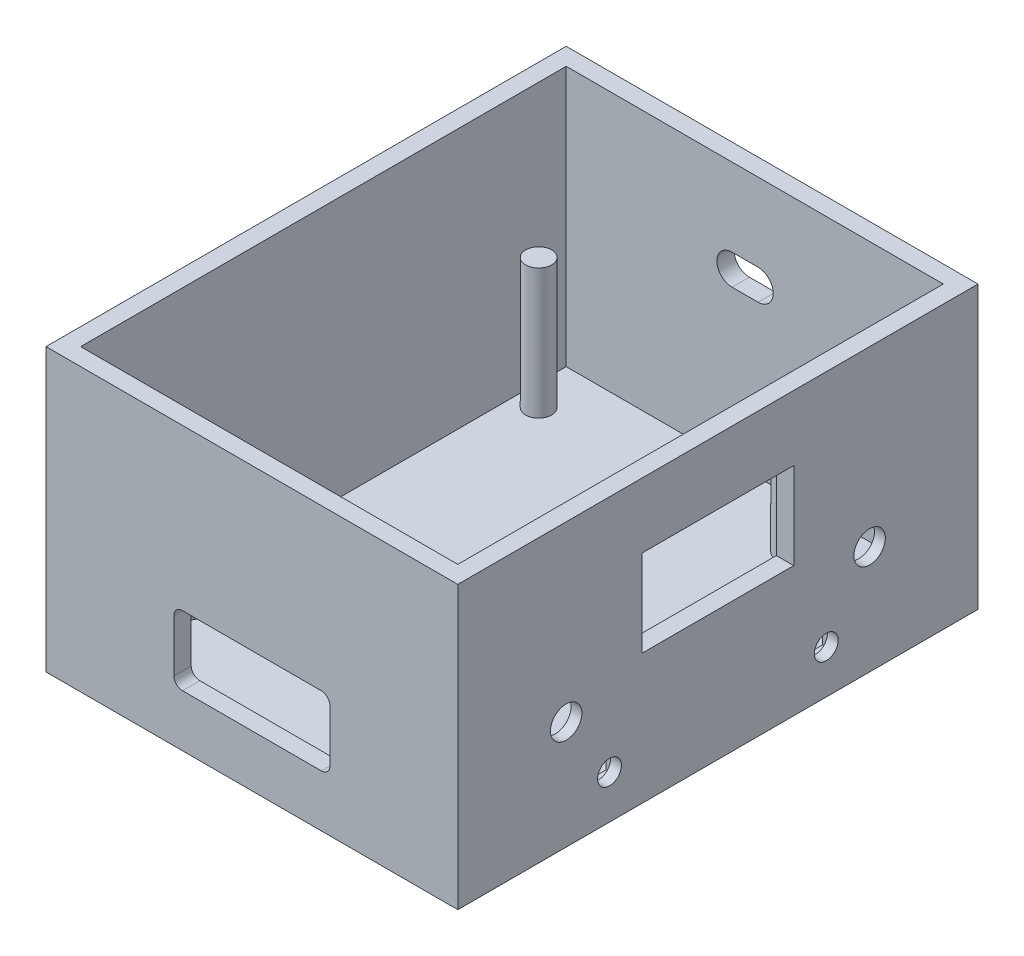
SolidWorks part; units mm, degrees
ref_plane "Front Plane" through (0, 0, 0) normal (0, 0, 1) x (1, 0, 0)
ref_plane "Top Plane" through (0, 0, 0) normal (0, 1, 0) x (1, 0, 0)
ref_plane "Right Plane" through (0, 0, 0) normal (1, 0, 0) x (0, 0, -1)
sketch "Sketch1" plane through (0, 0, 0) normal (0, 1, 0) x (1, 0, 0)
  line L1 (-47.5, -60) -> (47.5, -60)
  line L2 (-47.5, -60) -> (-47.5, 60)
  line L3 (-47.5, 60) -> (47.5, 60)
  line L4 (47.5, -60) -> (47.5, 60)
  line L5 (-47.5, -60) -> (47.5, 60) construction
  line L6 (-47.5, 60) -> (47.5, -60) construction
  point P0 (0, 0)
  dimension "D1" = 120
  dimension "D2" = 95
extrude "base dimensions" add sketch "Sketch1" along normal blind 5
sketch "Sketch2" plane through (0, 5, 0) normal (0, 1, 0) x (1, 0, 0)
  line L0 (47.5, -60) -> (47.5, 60) construction
  line L1 (-47.5, -60) -> (47.5, -60) construction
  line L2 (-47.5, 60) -> (-47.5, -60) construction
  line L3 (47.5, 60) -> (-47.5, 60) construction
  line L4 (47.5, -60) -> (47.5, 60)
  line L5 (-47.5, -60) -> (47.5, -60)
  line L6 (-47.5, 60) -> (-47.5, -60)
  line L7 (47.5, 60) -> (-47.5, 60)
  line L9 (-43.5, -56) -> (43.5, -56)
  line L10 (-43.5, -56) -> (-43.5, 56)
  line L11 (-43.5, 56) -> (43.5, 56)
  line L12 (43.5, -56) -> (43.5, 56)
  line L13 (-43.5, -56) -> (43.5, 56) construction
  line L14 (-43.5, 56) -> (43.5, -56) construction
  point P4 (0, 0)
  dimension "D1" = 4
  dimension "D2" = 4
extrude "wall height and depth" add sketch "Sketch2" along normal blind 60
sketch "Sketch3" plane through (0, 5, 0) normal (0, 1, 0) x (1, 0, 0)
  line L0 (-43.5, 56) -> (-43.5, -56) construction
  line L1 (-43.5, -56) -> (43.5, -56) construction
  circle A0 centre (-38.5, 44.645) radius 3
  circle A1 centre (-38.5, -36) radius 3
  circle A2 centre (32.62, -36) radius 3
  circle A3 centre (19.285, 44.645) radius 3
  dimension "D4" = 6
  dimension "D1" = 57.785
  dimension "D2" = 71.12
  dimension "D3" = 80.645
  dimension "D5" = 5
  dimension "D6" = 20
extrude "support pegs" add sketch "Sketch3" along normal blind 30
sketch "Sketch4" plane through (47.5, 0, 0) normal (1, 0, 0) x (0, 0, -1)
  line L0 (0, 71.0913) -> (0, -6.0913) construction
  line L1 (-17.5, 50) -> (17.5, 50)
  line L2 (-17.5, 50) -> (-17.5, 30)
  line L3 (-17.5, 30) -> (17.5, 30)
  line L4 (17.5, 50) -> (17.5, 30)
  line L5 (-17.5, 50) -> (17.5, 30) construction
  line L6 (-17.5, 30) -> (17.5, 50) construction
  line L7 (52.25, 0) -> (-52.25, 0) construction
  line L8 (-60, 65) -> (60, 65) construction
  circle A0 centre (-35, 25) radius 3.625
  circle A1 centre (-25, 10) radius 2.75
  circle A2 centre (25, 10) radius 2.75
  circle A3 centre (35, 25) radius 3.625
  point P0 (0, 40)
  point P12 (25, 10)
  dimension "D3" = 7.25
  dimension "D4" = 5.5
  dimension "D1" = 25
  dimension "D2" = 35
  dimension "D5" = 10
  dimension "D6" = 25
  dimension "D7" = 20
  dimension "D8" = 35
  dimension "D9" = 25
extrude "front holes" cut sketch "Sketch4" against normal up to surface (4 mm away) up to face at (43.5, 35, 0)
sketch "Sketch6" plane through (43.5, 0, 0) normal (-1, 0, 0) x (0, 0, 1)
  line L0 (0, -35.75) -> (0, 35.75) construction
  line L1 (-41.8, 31.5) -> (-28.2, 31.5)
  line L2 (-41.8, 31.5) -> (-41.8, 18.5)
  line L3 (-41.8, 18.5) -> (-28.2, 18.5)
  line L4 (-28.2, 31.5) -> (-28.2, 18.5)
  line L5 (-41.8, 31.5) -> (-28.2, 18.5) construction
  line L6 (-41.8, 18.5) -> (-28.2, 31.5) construction
  line L7 (-28.15, 6.85) -> (-21.85, 6.85)
  line L8 (-28.15, 6.85) -> (-28.15, 13.15)
  line L9 (-28.15, 13.15) -> (-21.85, 13.15)
  line L10 (-21.85, 6.85) -> (-21.85, 13.15)
  line L11 (-28.15, 6.85) -> (-21.85, 13.15) construction
  line L12 (-28.15, 13.15) -> (-21.85, 6.85) construction
  line L13 (28.15, 13.15) -> (21.85, 6.85) construction
  line L14 (28.15, 6.85) -> (21.85, 13.15) construction
  line L15 (41.8, 18.5) -> (28.2, 31.5) construction
  line L16 (41.8, 31.5) -> (28.2, 18.5) construction
  line L17 (21.85, 6.85) -> (21.85, 13.15)
  line L18 (28.15, 13.15) -> (21.85, 13.15)
  line L19 (28.15, 6.85) -> (28.15, 13.15)
  line L20 (28.15, 6.85) -> (21.85, 6.85)
  line L21 (28.2, 31.5) -> (28.2, 18.5)
  line L22 (41.8, 18.5) -> (28.2, 18.5)
  line L23 (41.8, 31.5) -> (41.8, 18.5)
  line L24 (41.8, 31.5) -> (28.2, 31.5)
  point P0 (-35, 25)
  point P6 (-25, 10)
  point P22 (25, 10)
  point P23 (35, 25)
  dimension "D1" = 13.6
  dimension "D2" = 13
  dimension "D3" = 6.3
extrude "en and b inlay" cut sketch "Sketch6" against normal blind 1.5
sketch "screen mounting layout" plane through (43.5, 0, 0) normal (-1, 0, 0) x (0, 0, 1)
  line L0 (0, -35.75) -> (0, 35.75) construction
  line L8 (-15.265, 24.85) -> (15.265, 24.85) construction
  line L9 (-15.265, 24.85) -> (-15.265, 53.46) construction
  line L10 (-15.265, 53.46) -> (15.265, 53.46) construction
  line L11 (15.265, 24.85) -> (15.265, 53.46) construction
  line L12 (-15.265, 24.85) -> (15.265, 53.46) construction
  line L13 (-15.265, 53.46) -> (15.265, 24.85) construction
  line L14 (-15.265, 23.3) -> (15.265, 23.3) construction
  line L15 (17.5, 30) -> (-17.5, 30) construction
  circle A0 centre (-15.265, 53.46) radius 1.55 construction
  circle A1 centre (-15.265, 24.85) radius 1.55 construction
  circle A2 centre (15.265, 24.85) radius 1.55 construction
  circle A3 centre (15.265, 53.46) radius 1.55 construction
  point P8 (0, 39.155)
  dimension "D3" = 3.1
  dimension "D4" = 3.1
  dimension "D1" = 30.53
  dimension "D2" = 28.61
  dimension "D5" = 6.7
sketch "Sketch9" plane through (0, 0, -56) normal (0, 0, 1) x (1, 0, 0)
  line L0 (-5.236, 43.5) -> (0.764, 43.5) construction
  line L1 (-5.236, 47) -> (0.764, 47)
  line L2 (-5.236, 40) -> (0.764, 40)
  line L3 (43.5, 5) -> (-43.5, 5) construction
  line L4 (-43.5, 65) -> (-43.5, 5) construction
  arc A0 (-5.236, 47) -> (-5.236, 40) centre (-5.236, 43.5) ccw
  arc A1 (0.764, 40) -> (0.764, 47) centre (0.764, 43.5) ccw
  point P2 (-2.236, 43.5)
  dimension "D2" = 3.5
  dimension "D1" = 6
  dimension "D3" = 35
  dimension "D4" = 41.264
extrude "usb slot" cut sketch "Sketch9" against normal through all
sketch "Sketch10" plane through (0, 0, 56) normal (0, 0, -1) x (-1, 0, 0)
  line L0 (52.25, 0) -> (-52.25, 0) construction
  line L1 (-18, 12) -> (18, 12)
  line L2 (-18, 12) -> (-18, 28)
  line L3 (-18, 28) -> (18, 28)
  line L4 (18, 12) -> (18, 28)
  line L5 (-18, 12) -> (18, 28) construction
  line L6 (-18, 28) -> (18, 12) construction
  line L7 (47.5, 65) -> (47.5, 0) construction
  point P0 (0, 20)
  point P5 (0, 24.618)
  point P6 (0, 22.6055)
  dimension "D1" = 20
  dimension "D2" = 36
  dimension "D3" = 16
  dimension "D4" = 47.5
extrude "Cut-Extrude1" cut sketch "Sketch10" against normal blind 10
fillet "Fillet1" radius 2 4 edges at (-18, 28, 58) (-18, 12, 58) (18, 28, 58) (18, 12, 58)
